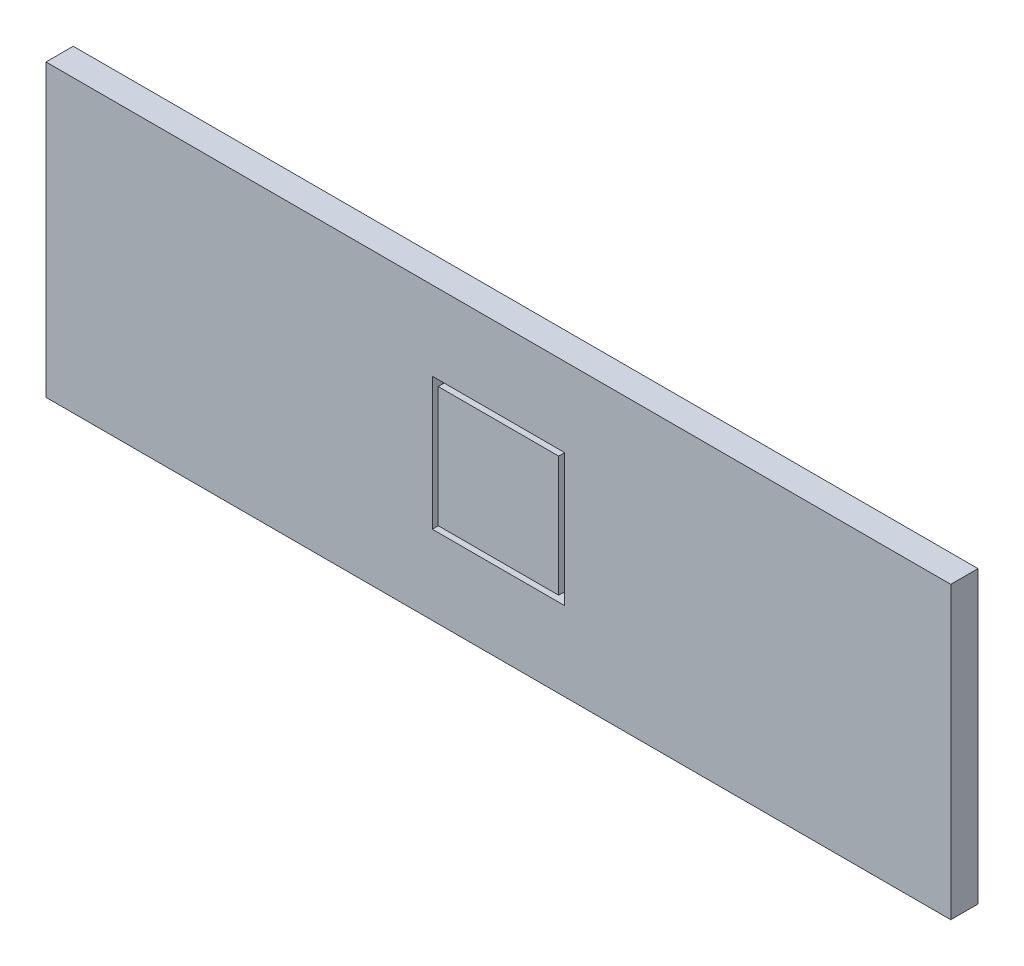
SolidWorks part; units mm, degrees
ref_plane "Front Plane" through (0, 0, 0) normal (0, 0, 1) x (1, 0, 0)
ref_plane "Top Plane" through (0, 0, 0) normal (0, 1, 0) x (1, 0, 0)
ref_plane "Right Plane" through (0, 0, 0) normal (1, 0, 0) x (0, 0, -1)
sketch "Sketch1" plane through (0, 0, 0) normal (0, 0, 1) x (1, 0, 0)
  line L1 (299, -96) -> (-299, -96)
  line L2 (299, -96) -> (299, 96)
  line L3 (299, 96) -> (-299, 96)
  line L4 (-299, -96) -> (-299, 96)
  line L5 (299, -96) -> (-299, 96) construction
  line L6 (299, 96) -> (-299, -96) construction
  point P0 (0, 0)
  dimension "D1" = 192
  dimension "D2" = 598
extrude "Boss-Extrude1" add sketch "Sketch1" along normal blind 18
sketch "Sketch2" plane through (0, 0, 18) normal (0, 0, 1) x (1, 0, 0)
  line L1 (43.7, -43.8) -> (-43.7, -43.8)
  line L2 (43.7, -43.8) -> (43.7, 43.8)
  line L3 (43.7, 43.8) -> (-43.7, 43.8)
  line L4 (-43.7, -43.8) -> (-43.7, 43.8)
  line L5 (43.7, -43.8) -> (-43.7, 43.8) construction
  line L6 (43.7, 43.8) -> (-43.7, -43.8) construction
  line L7 (39.8232, -39.8232) -> (-39.8232, -39.8232)
  line L8 (39.8232, -39.8232) -> (39.8232, 39.8232)
  line L9 (39.8232, 39.8232) -> (-39.8232, 39.8232)
  line L10 (-39.8232, -39.8232) -> (-39.8232, 39.8232)
  line L11 (35.5354, -35.6167) -> (-34.8361, 34.9158) construction
  line L12 (35.226, 35.226) -> (-35.226, -35.226) construction
  line L13 (35.226, 35.226) -> (-35.226, -35.226) construction
  line L14 (35.5354, -35.6167) -> (-34.8361, 34.9158) construction
  line L15 (39.8232, 39.8232) -> (-39.8232, -39.8232) construction
  line L16 (39.8232, -39.8232) -> (-39.8232, 39.8232) construction
  line L17 (39.8232, -39.8232) -> (-39.8232, 39.8232) construction
  line L18 (39.8232, 39.8232) -> (-39.8232, -39.8232) construction
  point P0 (0, 0)
  point P6 (0, 0)
  point P11 (0, 0)
  point P12 (0, 0)
  point P17 (0, 0)
  dimension "D1" = 87.4
  dimension "D2" = 87.6
extrude "Cut-Extrude1" cut sketch "Sketch2" against normal blind 7
sketch "Sketch3" plane through (0, 0, 11) normal (0, 0, 1) x (1, 0, 0)
  line L0 (-30, 33.8) -> (-43.7, 33.8) construction
  line L1 (30, -33.2) -> (-30, -33.2)
  line L2 (30, -33.2) -> (30, -5.099)
  line L3 (30, 33.8) -> (-30, 33.8)
  line L4 (-30, -33.2) -> (-30, -5.099)
  line L5 (30, -33.2) -> (-30, 33.8) construction
  line L6 (30, 33.8) -> (-30, -33.2) construction
  line L8 (-43.7, 43.8) -> (-43.7, -43.8) construction
  line L9 (30, 33.8) -> (43.7, 33.8) construction
  line L10 (43.7, -43.8) -> (43.7, 43.8) construction
  line L11 (43.7, 43.8) -> (-43.7, 43.8) construction
  line L12 (43.7, -43.8) -> (43.7, 43.8) construction
  line L13 (26.1638, -28.9162) -> (-26.1638, -28.9162)
  line L14 (26.1638, -28.9162) -> (26.1638, -8.0934)
  line L15 (26.1638, 29.5162) -> (-26.1638, 29.5162)
  line L16 (-26.1638, -28.9162) -> (-26.1638, -8.0934)
  line L17 (26.1638, -28.9162) -> (-26.1638, 29.5162) construction
  line L18 (26.1638, 29.5162) -> (-26.1638, -28.9162) construction
  line L19 (-19.9201, -0.1) -> (17.2276, -0.1) construction
  line L20 (0, 20.3492) -> (0, -19.8825) construction
  line L21 (-30, 4.899) -> (-30, 33.8)
  line L22 (-26.1638, 7.8934) -> (-26.1638, 29.5162)
  line L23 (26.1638, 7.8934) -> (26.1638, 29.5162)
  line L24 (30, 4.899) -> (30, 33.8)
  arc A4 (-30, -5.099) -> (-30, 4.899) centre (-30.2, -0.1) ccw
  arc A5 (-26.1638, -8.0934) -> (-26.1638, 7.8934) centre (-30.2, -0.1) ccw
  arc A6 (30, 4.899) -> (30, -5.099) centre (30.2, -0.1) ccw
  arc A7 (26.1638, 7.8934) -> (26.1638, -8.0934) centre (30.2, -0.1) ccw
  point P0 (0, 0.3)
  point P8 (0, 0.3)
  dimension "D1" = 60
  dimension "D2" = 67
  dimension "D3" = 10
  dimension "D5" = 13.5
extrude "Cut-Extrude2" cut sketch "Sketch3" against normal blind 10.5
sketch3d "Sketch_MAC1-1_KITCHLED_MILLING" [suppressed]
  line L0 (0, 0, 18) -> (10, 0, 18)
  line L1 (0, 0, 18) -> (0, 10, 18)
  point P0 (0, 0, 18)
  point P1 (10, 0, 18)
  point P2 (0, 10, 18)
sketch3d "Sketch_MAC1-2_KITCHLED_MILLING" [suppressed]
  line L0 (-43.25, -43.25, 18) -> (-33.25, -43.25, 18)
  line L1 (-43.25, -43.25, 18) -> (-43.25, -33.25, 18)
  point P0 (-43.25, -43.25, 18)
  point P1 (-33.25, -43.25, 18)
  point P2 (-43.25, -33.25, 18)
